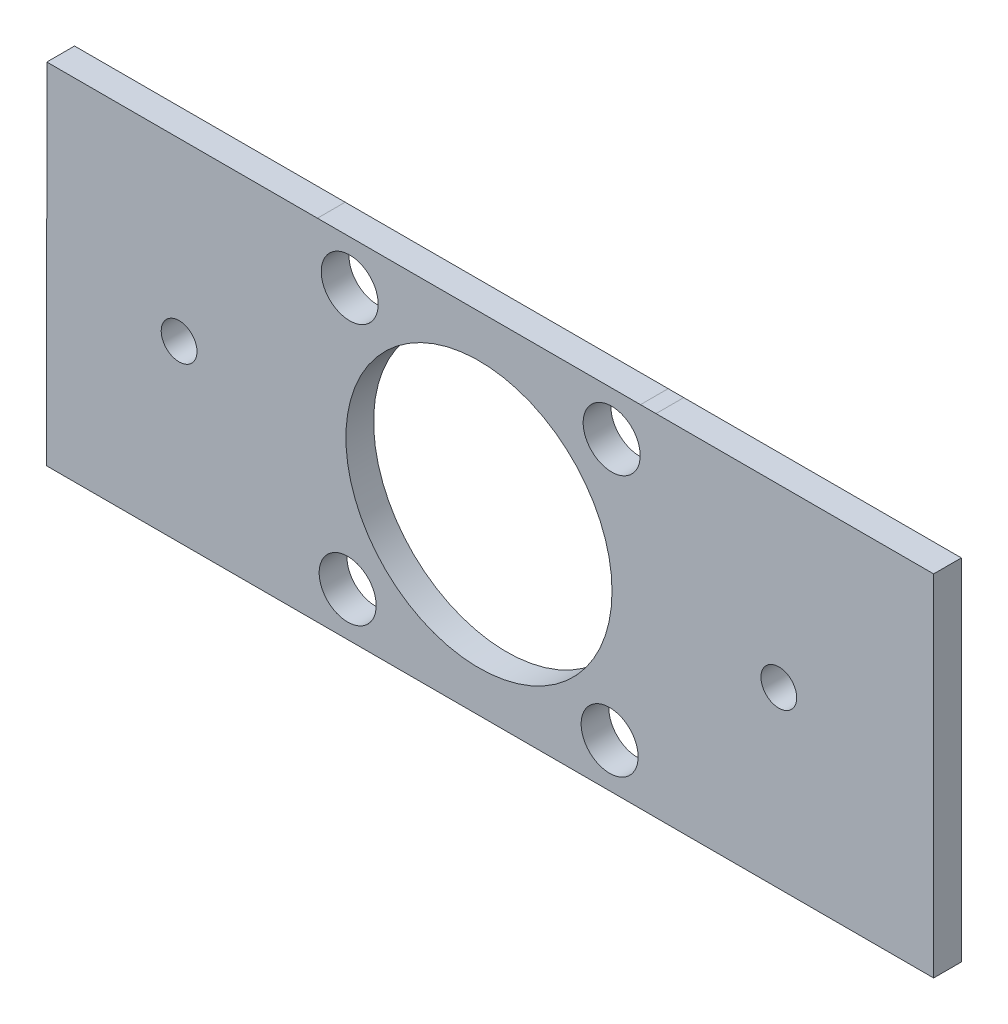
SolidWorks part; units mm, degrees
ref_plane "Front Plane" through (0, 0, 0) normal (0, 0, 1) x (1, 0, 0)
ref_plane "Top Plane" through (0, 0, 0) normal (0, 1, 0) x (1, 0, 0)
ref_plane "Right Plane" through (0, 0, 0) normal (1, 0, 0) x (0, 0, -1)
sketch "Model" plane through (0, 0, 0) normal (0, 0, 1) x (1, 0, 0)
  line L0 (52.7807, 19.962) -> (84.5747, 19.962)
  line L1 (84.5747, -20.1175) -> (52.8004, -20.1175)
  line L2 (84.5747, 19.962) -> (84.5747, -20.1175)
  line L3 (12.2189, -0.2598) -> (12.2189, 19.9554) construction
  line L4 (12.2189, -0.2598) -> (52.7906, -0.0777) construction
  line L12 (12.2189, -0.2598) -> (12.2189, -20.1111) construction
  line L20 (52.8004, -20.1175) -> (52.7807, 19.962) construction
  line L21 (52.7807, 19.962) -> (51.0027, 19.9621)
  line L22 (51.0027, 19.9621) -> (14.0068, 19.9557)
  line L23 (14.0068, 19.9557) -> (-16.9853, 19.95)
  line L25 (-17.0051, -20.1157) -> (13.987, -20.1109)
  line L26 (13.987, -20.1109) -> (51.0224, -20.1109)
  line L27 (51.0224, -20.1109) -> (52.8004, -20.1175)
  line L32 (32.5047, 19.9589) -> (32.5047, -20.1109) construction
  line L33 (-16.9853, 19.95) -> (-17.0051, -20.1157)
  circle A4 centre (17.7032, 14.8903) radius 3.2639
  circle A5 centre (47.7032, 14.893) radius 3.2639
  circle A6 centre (17.4693, -15.1072) radius 3.2639
  circle A7 centre (47.4692, -15.106) radius 3.2639
  circle A8 centre (32.5047, -0.1688) radius 15.24
  dimension "D24" = 30.48
  dimension "D3" = 52.07
  dimension "D4" = 49.5
  dimension "D7" = 1.778
  dimension "D8" = 1.778
  dimension "D9" = 29.9999
  dimension "D10" = 29.9999
  dimension "D13" = 5.066
  dimension "D15" = 5.08
  dimension "D18" = 29.9999
extrude "Boss-Extrude1" add sketch "Model" against normal blind 3.175
sketch "Sketch1" plane through (0, 0, -3.175) normal (0, 0, -1) x (-1, 0, 0)
  circle A0 centre (1.8356, -0.1688) radius 2.0497
  circle A1 centre (-66.8451, -0.1688) radius 2.0497
extrude "Cut-Extrude1" cut sketch "Sketch1" against normal through all
